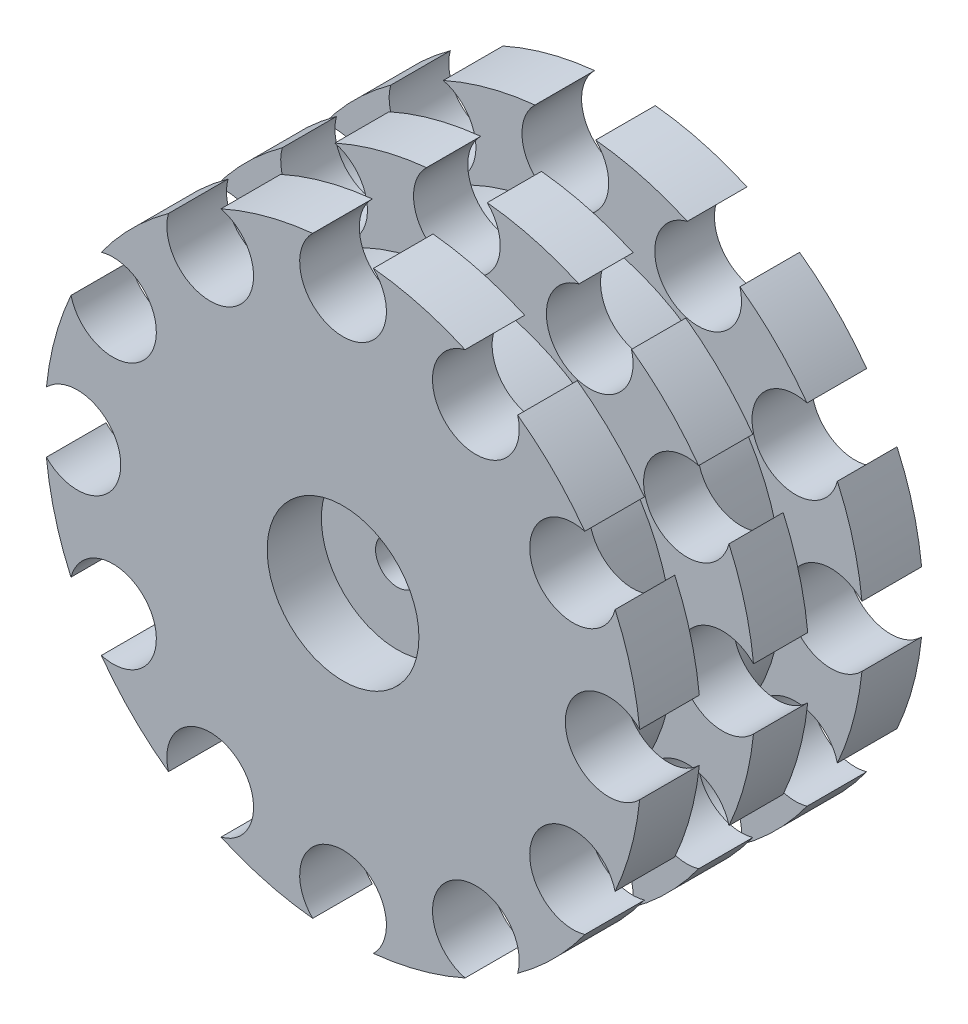
SolidWorks part; units mm, degrees
material "ABS"
ref_plane "Alzado" through (0, 0, 0) normal (0, 0, 1) x (1, 0, 0)
ref_plane "Planta" through (0, 0, 0) normal (0, 1, 0) x (1, 0, 0)
ref_plane "Vista lateral" through (0, 0, 0) normal (1, 0, 0) x (0, 0, -1)
sketch "Croquis1" plane through (0, 0, 0) normal (0, 1, 0) x (1, 0, 0)
  line L0 (0, 0) -> (0, 50000) construction
  line L1 (0, 1.5) -> (0, -9.5)
  line L3 (7, -9.5) -> (7, -13)
  line L4 (0, -9.5) -> (7, -9.5)
  line L5 (12.5, 13) -> (27.5, 13)
  line L6 (27.5, 13) -> (27.5, 7.5)
  line L7 (27.5, -2.5) -> (27.5, 2.5)
  line L8 (27.5, 2.5) -> (20, 2.5)
  line L9 (20, 2.5) -> (20, 7.5)
  line L10 (20, 7.5) -> (27.5, 7.5)
  line L12 (20, -7.5) -> (27.5, -7.5)
  line L13 (20, -2.5) -> (20, -7.5)
  line L14 (27.5, -2.5) -> (20, -2.5)
  line L15 (27.5, -13) -> (27.5, -7.5)
  line L16 (12.5, -13) -> (27.5, -13)
  line L27 (0, 1.5) -> (7.5, 1.5)
  line L28 (7.5, 1.5) -> (0, 1.5) construction
  line L29 (12.5, 6.5) -> (12.5, 13)
  line L32 (7, -13) -> (12.5, -13)
  line L37 (12.5, 6.5) -> (7.5, 1.5)
  line L38 (12.5, 6.5) -> (12.5, 13) construction
  point P22 (27.5, 0)
revolve "Revolución1" add sketch "Croquis1" angle 360 about L0
sketch "Croquis2" plane through (0, 0, -1.5) normal (0, 0, -1) x (-1, 0, 0)
  line L1 (7.5056, 0) -> (3.7528, 6.5)
  line L2 (3.7528, 6.5) -> (-3.7528, 6.5)
  line L3 (-3.7528, 6.5) -> (-7.5056, 0)
  line L4 (-7.5056, 0) -> (-3.7528, -6.5)
  line L5 (-3.7528, -6.5) -> (3.7528, -6.5)
  line L6 (3.7528, -6.5) -> (7.5056, 0)
  circle A0 centre (0, 0) radius 6.5 construction
extrude "Cortar-Extruir1" cut sketch "Croquis2" against normal blind 9
sketch "Croquis5" plane through (0, 0, 13) normal (0, 0, 1) x (1, 0, 0)
  line L0 (0, 0) -> (0, 27.5) construction
  line L1 (0, 27.5) -> (0, 24.5) construction
  circle A0 centre (0, 0) radius 27.5 construction
  circle A1 centre (0, 24.5) radius 4
  circle A2 centre (12.25, 21.2176) radius 4
  circle A3 centre (21.2176, 12.25) radius 4
  circle A4 centre (24.5, 0) radius 4
  circle A5 centre (21.2176, -12.25) radius 4
  circle A6 centre (12.25, -21.2176) radius 4
  circle A7 centre (0, -24.5) radius 4
  circle A8 centre (-12.25, -21.2176) radius 4
  circle A9 centre (-21.2176, -12.25) radius 4
  circle A10 centre (-24.5, 0) radius 4
  circle A11 centre (-21.2176, 12.25) radius 4
  circle A12 centre (-12.25, 21.2176) radius 4
  point P33 (0, 0)
  dimension "D1" = 12
extrude "Cortar-Extruir3" cut sketch "Croquis5" against normal through all
sketch "Croquis6" plane through (0, 0, 7.5) normal (0, 0, -1) x (-1, 0, 0)
  circle A0 centre (0, 0) radius 2
extrude "Cortar-Extruir4" cut sketch "Croquis6" against normal blind 10
sketch "Croquis7" plane through (0, 0, 7.5) normal (0, 0, -1) x (-1, 0, 0)
  line L6 (3.7528, -6.5) -> (7.5056, 0)
  line L7 (7.5056, 0) -> (3.7528, 6.5)
  line L8 (3.7528, 6.5) -> (-3.7528, 6.5)
  line L9 (-3.7528, 6.5) -> (-7.5056, 0)
  line L10 (-7.5056, 0) -> (-3.7528, -6.5)
  line L11 (-3.7528, -6.5) -> (3.7528, -6.5)
  line L12 (3.7528, -6.5) -> (7.5056, 0)
  line L13 (7.5056, 0) -> (3.7528, 6.5)
  line L14 (3.7528, 6.5) -> (-3.7528, 6.5)
  line L15 (-3.7528, 6.5) -> (-7.5056, 0)
  line L16 (-7.5056, 0) -> (-3.7528, -6.5)
  line L17 (-3.7528, -6.5) -> (3.7528, -6.5)
  circle A0 centre (0, 0) radius 2
  dimension "D1" = 0
extrude "Saliente-Extruir1" add sketch "Croquis7" along normal blind 1.5
sketch "Croquis8" plane through (0, 0, 9.5) normal (0, 0, 1) x (1, 0, 0)
  circle A0 centre (0, 0) radius 2
  circle A1 centre (0, 0) radius 7
extrude "Cortar-Extruir5" cut sketch "Croquis8" against normal blind 1.5
